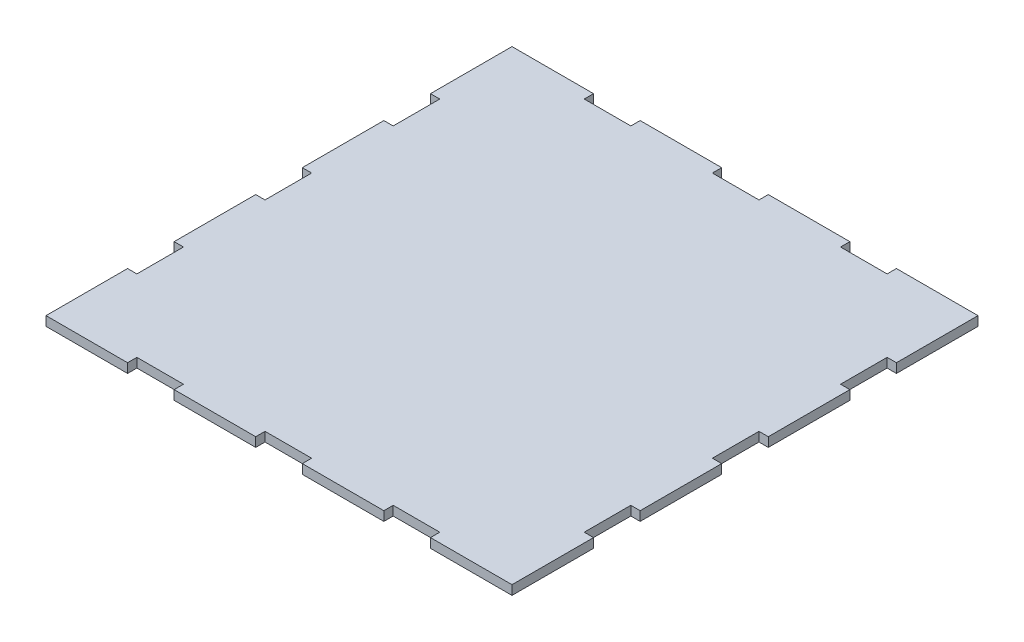
SolidWorks part; units mm, degrees
ref_plane "Plano frontal" through (0, 0, 0) normal (0, 0, 1) x (1, 0, 0)
ref_plane "Plano superior" through (0, 0, 0) normal (0, 1, 0) x (1, 0, 0)
ref_plane "Plano direito" through (0, 0, 0) normal (1, 0, 0) x (0, 0, -1)
sketch "Esboço1" plane through (0, 0, 0) normal (0, 1, 0) x (1, 0, 0)
  line L0 (-100, 100) -> (100, -100) construction
  line L1 (-100, 100) -> (100, 100)
  line L2 (-100, 100) -> (-100, -100)
  line L3 (-100, -100) -> (100, -100)
  line L4 (100, 100) -> (100, -100)
  point P4 (0, 0)
  dimension "D1" = 200
  dimension "D2" = 200
extrude "Ressalto-extrusão1" add sketch "Esboço1" along normal blind 4
sketch "Esboço2" plane through (0, 4, 0) normal (0, 1, 0) x (1, 0, 0)
  line L0 (-65, 100) -> (-65, 96)
  line L1 (100, -65) -> (96, -65)
  line L2 (100, 100) -> (-100, 100) construction
  line L3 (-65, 96) -> (-45, 96)
  line L4 (-45, 96) -> (-45, 100)
  line L5 (-45, 100) -> (-10, 100)
  line L6 (-10, 100) -> (-10, 96)
  line L7 (-10, 96) -> (10, 96)
  line L8 (10, 96) -> (10, 100)
  line L9 (10, 100) -> (45, 100)
  line L10 (45, 100) -> (45, 96)
  line L11 (45, 96) -> (65, 96)
  line L12 (65, 96) -> (65, 100)
  line L13 (-100, 100) -> (-100, -100) construction
  line L14 (100, -100) -> (100, 100) construction
  line L15 (96, -65) -> (96, -45)
  line L16 (-65, 100) -> (-45, 100)
  line L17 (-10, 100) -> (10, 100)
  line L18 (45, 100) -> (65, 100)
  line L19 (96, -45) -> (100, -45)
  line L20 (100, 45) -> (100, 10)
  line L21 (100, 10) -> (96, 10)
  line L22 (96, 10) -> (96, -10)
  line L23 (96, -10) -> (100, -10)
  line L24 (100, -10) -> (100, -45)
  line L25 (100, 45) -> (96, 45)
  line L26 (96, 45) -> (96, 65)
  line L27 (96, 65) -> (100, 65)
  line L28 (-100, -100) -> (100, -100) construction
  line L29 (100, 65) -> (100, 45)
  line L31 (100, -45) -> (100, -65)
  line L32 (0, 100) -> (0, -100) construction
  line L33 (100, 10) -> (100, -10)
  line L35 (-100, 10) -> (-100, -10)
  line L40 (-100, -45) -> (-100, -65)
  line L44 (-100, 65) -> (-100, 45)
  line L50 (-96, 65) -> (-100, 65)
  line L51 (-96, 45) -> (-96, 65)
  line L52 (-100, 45) -> (-96, 45)
  line L53 (-100, -10) -> (-100, -45)
  line L54 (-96, -10) -> (-100, -10)
  line L55 (-96, 10) -> (-96, -10)
  line L56 (-100, 10) -> (-96, 10)
  line L57 (-100, 45) -> (-100, 10)
  line L58 (-96, -45) -> (-100, -45)
  line L59 (-96, -65) -> (-96, -45)
  line L60 (-100, -65) -> (-96, -65)
  line L61 (-100, 0) -> (100, 0) construction
  line L62 (45, -100) -> (65, -100)
  line L63 (-10, -100) -> (10, -100)
  line L64 (-65, -100) -> (-45, -100)
  line L65 (65, -96) -> (65, -100)
  line L66 (45, -96) -> (65, -96)
  line L67 (45, -100) -> (45, -96)
  line L68 (10, -100) -> (45, -100)
  line L69 (10, -96) -> (10, -100)
  line L70 (-10, -96) -> (10, -96)
  line L71 (-10, -100) -> (-10, -96)
  line L72 (-45, -100) -> (-10, -100)
  line L73 (-45, -96) -> (-45, -100)
  line L74 (-65, -96) -> (-45, -96)
  line L75 (-65, -100) -> (-65, -96)
  line M9 (-100, 100) -> (-100, -100)
  line M10 (-100, -100) -> (100, -100)
  line M11 (100, -100) -> (100, 100)
  line M12 (100, 100) -> (-100, 100)
  dimension "D1" = 20
  dimension "D2" = 20
  dimension "D3" = 20
  dimension "D4" = 35
  dimension "D5" = 35
  dimension "D6" = 35
  dimension "D7" = 4
  dimension "D8" = 20
  dimension "D9" = 35
  dimension "D10" = 20
  dimension "D11" = 35
  dimension "D12" = 20
  dimension "D13" = 35
  dimension "D14" = 4
extrude "Corte-extrusão1" cut sketch "Esboço2" against normal through all contours L56 L54 L55 M9 | L71 L69 L70 M10 | L22 L23 L21 M11 | L7 L8 L6 M12
